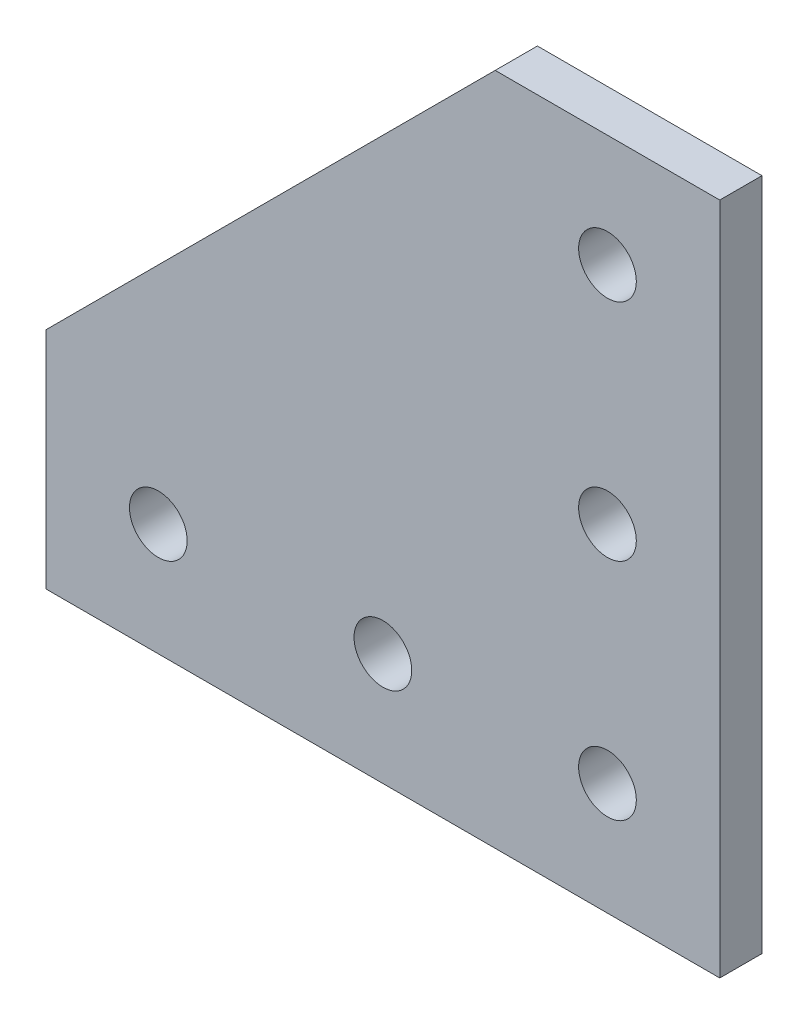
SolidWorks part; units mm, degrees
ref_plane "Front Plane" through (0, 0, 0) normal (0, 0, 1) x (1, 0, 0)
ref_plane "Top Plane" through (0, 0, 0) normal (0, 1, 0) x (1, 0, 0)
ref_plane "Right Plane" through (0, 0, 0) normal (1, 0, 0) x (0, 0, -1)
ref_plane "Plane1" through (0, 0, 0) normal (0, 0, 1) x (1, 0, 0)
sketch "Sketch1" plane through (0, 0, 0) normal (0, 0, 1) x (1, 0, 0)
  line L0 (-63.5, -12.7) -> (12.7, -12.7)
  line L1 (12.7, -12.7) -> (12.7, 63.5)
  line L2 (12.7, 63.5) -> (-12.7, 63.5)
  line L3 (-12.7, 63.5) -> (-63.5, 12.7)
  line L4 (-63.5, 12.7) -> (-63.5, -12.7)
  circle A0 centre (0, 50.8) radius 3.2639
  circle A1 centre (0, 25.4) radius 3.2639
  circle A2 centre (0, 0) radius 3.2639
  circle A3 centre (-25.4, 0) radius 3.2639
  circle A4 centre (-50.8, 0) radius 3.2639
  point P15 (-63.5, 0)
  point P16 (0, 63.5)
extrude "Boss-Extrude1" add sketch "Sketch1" along normal blind 4.7752
